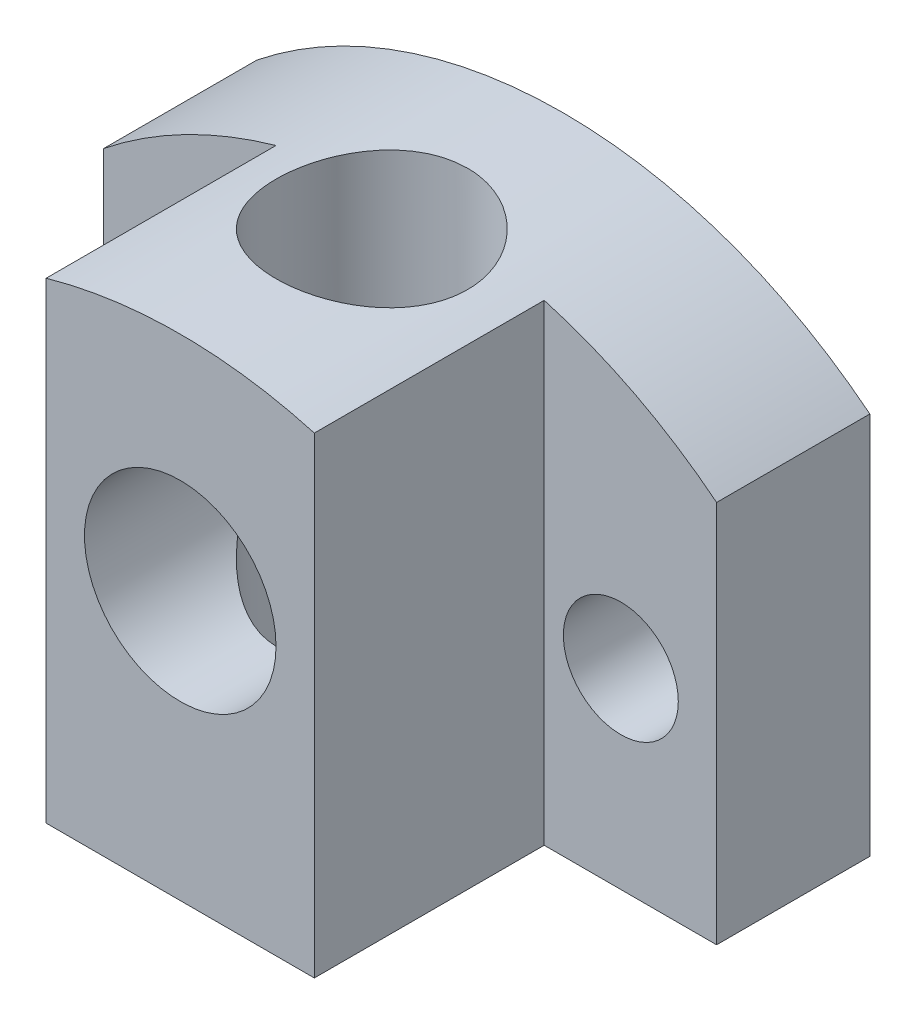
SolidWorks part; units mm, degrees
ref_plane "前视基准面" through (0, 0, 0) normal (0, 0, 1) x (1, 0, 0)
ref_plane "上视基准面" through (0, 0, 0) normal (0, 1, 0) x (1, 0, 0)
ref_plane "右视基准面" through (0, 0, 0) normal (1, 0, 0) x (0, 0, -1)
sketch "草图1" plane through (0, 0, 0) normal (0, 1, 0) x (1, 0, 0)
  line L0 (0, 43.4622) -> (0, -56.5378) construction
  line L1 (-80, 43.4622) -> (80, 43.4622)
  line L2 (-80, 43.4622) -> (-80, 3.4622)
  line L3 (-80, 3.4622) -> (80, 3.4622)
  line L4 (80, 43.4622) -> (80, 3.4622)
  line L5 (-35, 3.4622) -> (35, 3.4622)
  line L6 (-35, 3.4622) -> (-35, -56.5378)
  line L7 (-35, -56.5378) -> (35, -56.5378)
  line L8 (35, 3.4622) -> (35, -56.5378)
  circle A0 centre (0, -6.5378) radius 25
  point P8 (0, 43.4622)
  point P9 (0, -48.5378)
  point P14 (0, 0)
  point P15 (0, 0)
  point P16 (0, 0)
  point P17 (0, 0)
  point P18 (0, 0)
  point P19 (0, -12.3074)
  point P20 (0, 0)
  point P21 (0, 0)
  dimension "D1" = 50
sketch "草图2" plane through (0, 0, 0) normal (0, 0, 1) x (1, 0, 0)
  line L1 (-35, 0) -> (35, 0)
  line L2 (-35, 0) -> (-35, 123.1868)
  line L4 (35, 0) -> (35, 123.1868)
  line L5 (-80, 0) -> (80, 0) construction
  line L6 (-80, 0) -> (80, 0)
  line L7 (-80, 0) -> (-80, 100)
  line L9 (80, 0) -> (80, 100)
  line L10 (-80, 0) -> (80, 0) construction
  line L11 (0, 0) -> (0, 128.0625) construction
  arc A0 (-80, 100) -> (80, 100) centre (0, 0) cw
  arc A1 (35, 123.1868) -> (-35, 123.1868) centre (0, 0.2797) ccw
  point P5 (0, 0)
  point P14 (0, 0)
  point P17 (0, 0)
  point P19 (0, 0)
ref_plane "基准面1" through (0, 0, -3.4622) normal (0, 0, 1) x (1, 0, 0)
extrude "凸台-拉伸1" add sketch "草图2" against normal blind 40 from surface at -3.4622 contours L7 A0 L9 L6 starting at plane "基准面1"
sketch "草图4" plane through (0, 0, -3.4622) normal (0, 0, 1) x (1, 0, 0)
  line L0 (-35, 0) -> (-35, 123.1868)
  line L1 (-80, 0) -> (80, 0) construction
  line L2 (-35, 0) -> (35, 0) construction
  line L4 (35, 123.1868) -> (35, 0)
  line L5 (35, 0) -> (-35, 0)
  arc A0 (80, 100) -> (-80, 100) centre (0, 0) ccw construction
  arc A1 (35, 123.1868) -> (-35, 123.1868) centre (0, 0) ccw
extrude "凸台-拉伸2" add sketch "草图4" along normal blind 60
extrude "切除-拉伸1" cut sketch "草图1" along normal up to surface (128.0625 mm away) contours A0
sketch "草图5" plane through (0, 0, -3.4622) normal (0, 0, 1) x (1, 0, 0)
  line L0 (0, 0) -> (0, 128.0625) construction
  line L1 (-35, 0) -> (35, 0) construction
  line L2 (-80, 0) -> (-35, 0) construction
  line L3 (-55, 0) -> (-55, 115.6503) construction
  arc A0 (35, 123.1868) -> (-35, 123.1868) centre (0, 0) ccw construction
  circle A1 centre (0, 70) radius 25
  arc A2 (-35, 123.1868) -> (-80, 100) centre (0, 0) ccw construction
  circle A3 centre (-55, 50) radius 15
  circle A4 centre (55, 50) radius 15
  point P11 (-55, 0)
  dimension "D3" = 50
  dimension "D1" = 70
  dimension "D2" = 55
extrude "切除-拉伸2" cut sketch "草图5" against normal through all and the other way through all contours A4 | A3 | A1
